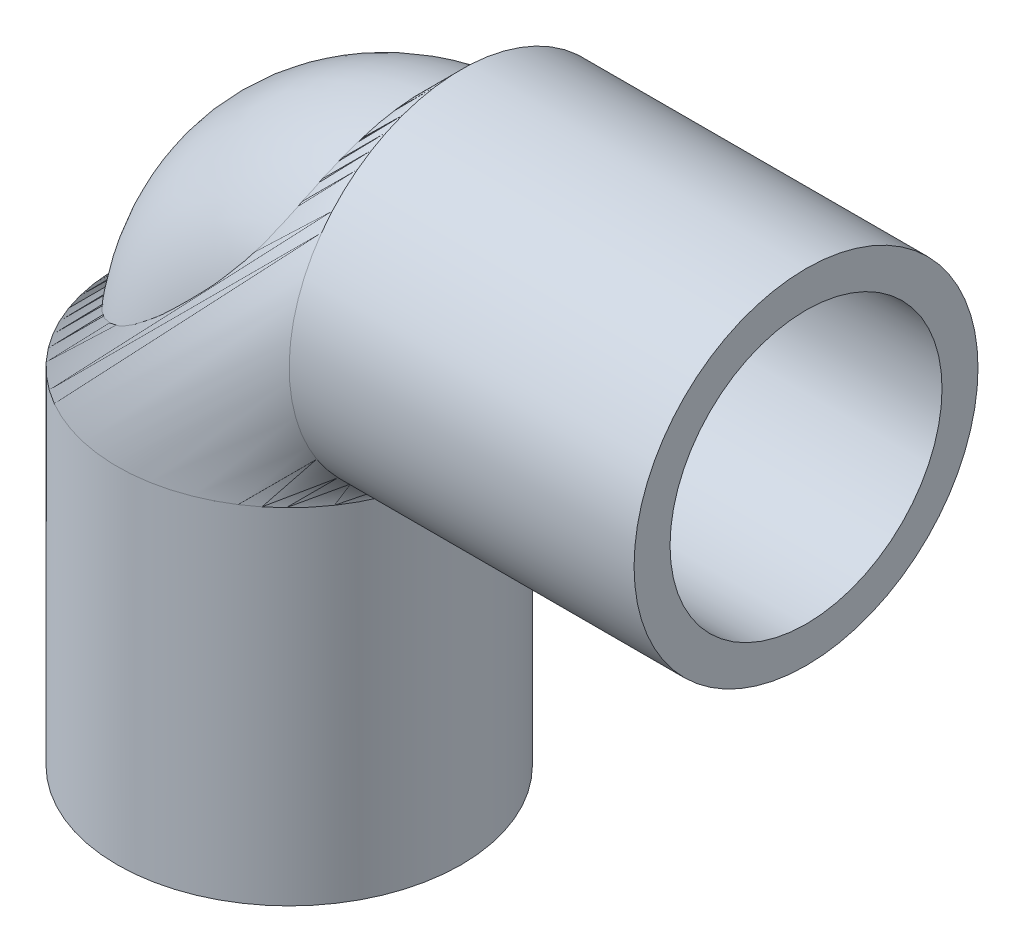
SolidWorks part; units mm, degrees
material "PVC Rigid"
ref_plane "Front Plane" through (0, 0, 0) normal (0, 0, 1) x (1, 0, 0)
ref_plane "Top Plane" through (0, 0, 0) normal (0, 1, 0) x (1, 0, 0)
ref_plane "Right Plane" through (0, 0, 0) normal (1, 0, 0) x (0, 0, -1)
sketch "Sketch1" plane through (0, 0, 0) normal (0, 1, 0) x (1, 0, 0)
  circle A0 centre (0, 0) radius 16.637
  circle A1 centre (0, 0) radius 13.1572
  dimension "D1" = 33.274
  dimension "D2" = 26.3144
sketch "Sketch4" plane through (0, 0, 0) normal (0, 0, 1) x (1, 0, 0)
  line L0 (0, 0) -> (0, 33.363)
  line L1 (16.637, 0) -> (-16.637, 0) construction
  line L2 (16.637, 50) -> (50, 50)
  arc A0 (0, 33.363) -> (16.637, 50) centre (16.637, 33.363) cw
  point P7 (0, 50)
  dimension "D3" = 16.637
  dimension "D1" = 50
  dimension "D2" = 50
sweep "Sweep4" add profiles "Sketch1" path "Sketch4"
